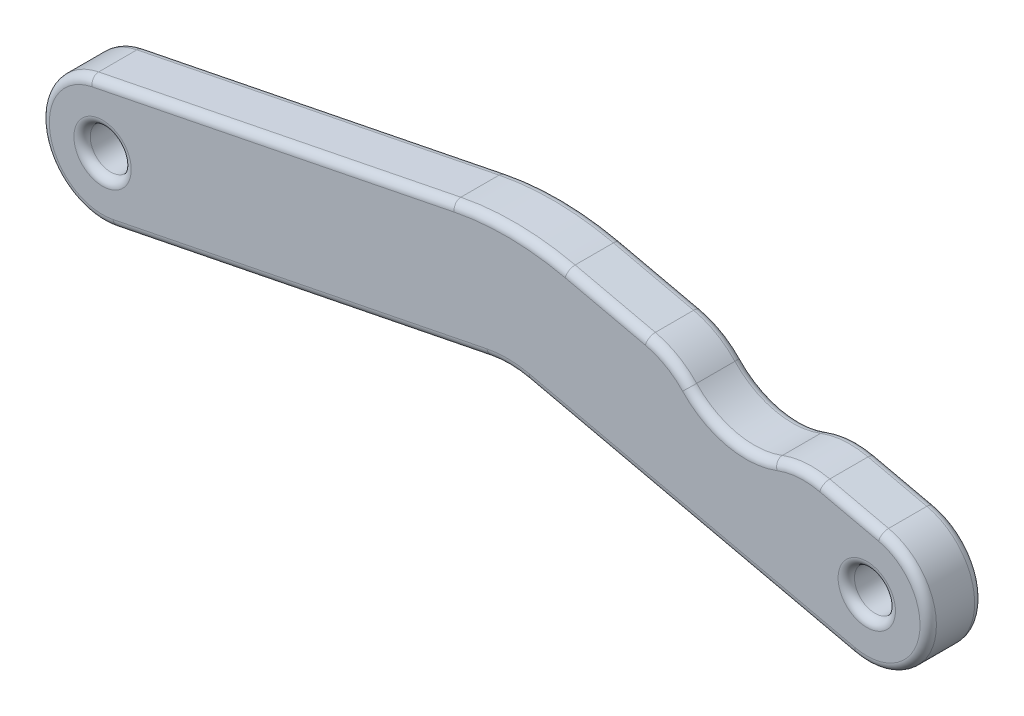
SolidWorks part; units mm, degrees
ref_plane "Front" through (0, 0, 0) normal (0, 0, 1) x (1, 0, 0)
ref_plane "Top" through (0, 0, 0) normal (0, 1, 0) x (1, 0, 0)
ref_plane "Right" through (0, 0, 0) normal (1, 0, 0) x (0, 0, -1)
sketch "Sketch1" plane through (0, 0, 0) normal (0, 0, 1) x (1, 0, 0)
  line L0 (0, 0) -> (27.9872, 0) construction
  line L1 (0, 2.25) -> (27.9872, 2.25)
  line L2 (0, -2.25) -> (27.9872, -2.25)
  circle A0 centre (0, 0) radius 0.75
  arc A1 (0, 2.25) -> (0, -2.25) centre (0, 0) ccw
  arc A2 (27.9872, -2.25) -> (27.9872, 2.25) centre (27.9872, 0) ccw
  circle A3 centre (27.9872, 0) radius 0.75
  point P3 (13.9936, 0)
  dimension "D1" = 1.5
  dimension "D2" = 27.9872
  dimension "D3" = 1.5
extrude "Boss-Extrude1" add sketch "Sketch1" along normal blind 2
sketch "Sketch2" plane through (0, 0, 0) normal (0, 0, 1) x (1, 0, 0)
  line L0 (12.0571, -0.5571) -> (14.4503, 0.4122)
  line L1 (15.3955, 0.2207) -> (16.4724, -0.5571)
  line L2 (16.4724, -0.5571) -> (17.3174, -2.6432)
  line L3 (17.3174, -2.6432) -> (12.0571, -3.2881)
  line L4 (12.0571, -3.2881) -> (12.0571, -0.5571)
  arc A0 (14.4503, 0.4122) -> (15.3955, 0.2207) centre (14.7783, -0.3977) cw
sketch "Sketch3" plane through (0, 0, 0) normal (0, 0, 1) x (1, 0, 0)
  line L0 (0.4422, -2.2061) -> (14.1398, 0.5393)
  line L1 (15.5781, 0.5204) -> (27.4873, -2.1937)
  line L2 (-0.4422, 2.2061) -> (12.8219, 4.8647)
  line L3 (17.0092, 4.8097) -> (28.4872, 2.1937)
  circle A0 centre (0, 0) radius 2.25 construction
  arc A1 (14.1398, 0.5393) -> (15.5781, 0.5204) centre (14.8148, -2.8286) cw
  arc A2 (27.4873, -2.1937) -> (28.4872, 2.1937) centre (27.9872, 0) ccw
  arc A3 (27.9872, -2.25) -> (27.9872, 2.25) centre (27.9872, 0) ccw construction
  circle A4 centre (27.9872, 0) radius 0.75 construction
  arc A5 (0.4422, -2.2061) -> (-0.4422, 2.2061) centre (0, 0) cw
  arc A6 (0, 2.25) -> (0, -2.25) centre (0, 0) ccw construction
  arc A7 (12.8219, 4.8647) -> (17.0092, 4.8097) centre (14.7871, -4.9403) cw
  dimension "D1" = 10
extrude "Cut-Extrude4" cut sketch "Sketch3" along normal through all flip side to cut
sketch "Sketch4" plane through (0, 0, 2) normal (0, 0, 1) x (1, 0, 0)
  line L4 (12.8219, 4.8647) -> (-0.4422, 2.2061)
  line L5 (28.4872, 2.1937) -> (17.0092, 4.8097)
  line L6 (15.5781, 0.5204) -> (27.4873, -2.1937)
  line L7 (0.4422, -2.2061) -> (14.1398, 0.5393)
  line L8 (12.8219, 4.8647) -> (-0.4422, 2.2061)
  line L9 (28.4872, 2.1937) -> (17.0092, 4.8097)
  line L10 (15.5781, 0.5204) -> (27.4873, -2.1937)
  line L11 (0.4422, -2.2061) -> (14.1398, 0.5393)
  circle A0 centre (27.9872, 0) radius 0.75 construction
  circle A1 centre (0, 0) radius 0.75 construction
  circle A2 centre (27.9872, 0) radius 0.75
  circle A3 centre (0, 0) radius 0.75
  arc A4 (17.0092, 4.8097) -> (12.8219, 4.8647) centre (14.7871, -4.9403) ccw
  arc A5 (27.4873, -2.1937) -> (28.4872, 2.1937) centre (27.9872, 0) ccw
  arc A6 (15.5781, 0.5204) -> (14.1398, 0.5393) centre (14.8148, -2.8286) ccw
  arc A7 (-0.4422, 2.2061) -> (0.4422, -2.2061) centre (0, 0) ccw
  arc A8 (17.0092, 4.8097) -> (12.8219, 4.8647) centre (14.7871, -4.9403) ccw
  arc A9 (27.4873, -2.1937) -> (28.4872, 2.1937) centre (27.9872, 0) ccw
  arc A10 (15.5781, 0.5204) -> (14.1398, 0.5393) centre (14.8148, -2.8286) ccw
  arc A11 (-0.4422, 2.2061) -> (0.4422, -2.2061) centre (0, 0) ccw
  dimension "D1" = 0
extrude "Boss-Extrude2" add sketch "Sketch4" against normal up to vertex
sketch3d "3DSketch2"
  line L8 (28.5539, 2.4862, 2) -> (20.7366, 4.2679, 2)
  line L9 (30.5553, 5.4776, 2) -> (31.9718, 1.7671, 2)
  line L10 (18.1052, 9.4862, 2) -> (17.7608, 10.5197, 2)
  line L11 (20.8202, 8.9829, 2) -> (18.1052, 9.4862, 2)
  arc A18 (30.4787, 0.5435, 2) -> (28.5539, 2.4862, 2) centre (27.9872, 0, 2) ccw
  arc A19 (29.7103, 7.668, 2) -> (30.5553, 5.4776, 2) centre (-281.7577, -113.7456, 2) ccw
  arc A20 (25.106, 12.1538, 2) -> (29.7103, 7.668, 2) centre (22.4753, 4.8477, 2) ccw
  arc A21 (21.1241, 8.8735, 2) -> (20.8202, 8.9829, 2) centre (20.6379, 7.9997, 2) ccw
  arc A22 (26.5449, 8.4396, 2) -> (21.1241, 8.8735, 2) centre (23.5636, 5.2719, 2) ccw
  arc A23 (25.3798, 7.2017, 2) -> (26.5449, 8.4396, 2) centre (25.9623, 7.8207, 2) ccw
  arc A24 (21.6394, 7.094, 2) -> (25.3798, 7.2017, 2) centre (23.5636, 5.2719, 2) ccw
  arc A25 (20.9991, 6.8287, 2) -> (21.6394, 7.094, 2) centre (21.0222, 7.6784, 2) ccw
  arc A26 (20.7366, 4.2679, 2) -> (20.9991, 6.8287, 2) centre (23.5636, 5.2719, 2) ccw
  spline S12 degree 3 poles (31.0836, 0.7536, 2) (30.8819, 0.6835, 2) (30.6803, 0.6135, 2) (30.4787, 0.5435, 2) knots 0 0 0 0 1 1 1 1
  spline S13 degree 3 poles (31.9718, 1.7671, 2) (31.9394, 1.656, 2) (31.8982, 1.5432, 2) (31.793, 1.3329, 2) (31.7287, 1.2339, 2) (31.5778, 1.0565, 2) (31.4894, 0.9764, 2) (31.2983, 0.8449, 2) (31.195, 0.7923, 2) (31.0836, 0.7536, 2) knots 0 0 0 0 0.25 0.25 0.5 0.5 0.75 0.75 1 1 1 1
  spline S14 degree 3 poles (21.9785, 12.5206, 2) (22.5054, 12.5209, 2) (23.0298, 12.4877, 2) (24.0747, 12.3695, 2) (24.5956, 12.2784, 2) (25.106, 12.1538, 2) knots 0 0 0 0 0.5 0.5 1 1 1 1
  spline S15 degree 3 poles (21.2302, 12.2749, 2) (21.4793, 12.3579, 2) (21.7264, 12.4476, 2) (21.9785, 12.5206, 2) knots 0 0 0 0 1 1 1 1
  spline S16 degree 3 poles (19.5527, 11.5132, 2) (19.7933, 11.7049, 2) (20.0675, 11.854, 2) (20.6399, 12.0887, 2) (20.9367, 12.1771, 2) (21.2302, 12.2749, 2) knots 0 0 0 0 0.5 0.5 1 1 1 1
  spline S17 degree 3 poles (17.7608, 10.5197, 2) (18.4099, 10.7525, 2) (19.009, 11.0801, 2) (19.5527, 11.5132, 2) knots 0 0 0 0 1 1 1 1
  point P53 (27.9872, 0, 4.55)
  point P54 (-281.7577, -113.7456, -332.2957)
  point P55 (22.4753, 4.8477, -5.7653)
  point P56 (20.6379, 7.9997, 3)
  point P57 (23.5636, 5.2719, 6.35)
  point P58 (25.9623, 7.8207, 2.85)
  point P59 (23.5636, 5.2719, -0.65)
  point P60 (21.0222, 7.6784, 2.85)
  point P61 (23.5636, 5.2719, -1)
sketch "Sketch6" plane through (0, 0, 0) normal (0, 0, 1) x (1, 0, 0)
  line L0 (28.4872, 2.1937) -> (17.0092, 4.8097) construction
  line L1 (26.3336, 2.6846) -> (28.4872, 2.1937)
  line L2 (19.946, 4.1403) -> (18.7601, 4.4106)
  line L3 (18.7601, 4.4106) -> (19.0316, 7.1775)
  line L4 (19.0316, 7.1775) -> (29.1272, 6.3891)
  line L5 (29.1272, 6.3891) -> (28.4872, 2.1937)
  circle A0 centre (23.5636, 5.2719) radius 1
  circle A1 centre (23.5636, 5.2719) radius 2.5 construction
  arc A2 (21.4578, 3.278) -> (24.5974, 2.5625) centre (23.5636, 5.2719) ccw
  arc A3 (24.5974, 2.5625) -> (26.3336, 2.6846) centre (25.6669, -0.2404) cw
  arc A4 (21.4578, 3.278) -> (19.946, 4.1403) centre (19.2794, 1.2153) ccw
  point P13 (25.2699, 2.927)
  point P14 (0, 0)
  point P20 (21.0097, 3.8979)
  dimension "D1" = 2
  dimension "D2" = 1.5
  dimension "D3" = 3
  dimension "D4" = 3
  dimension "D5" = 0.4
extrude "Cut-Extrude6" cut sketch "Sketch6" against normal through all and the other way through all
fillet "Fillet1" radius 0.3 28 edges at (28.7372, 0, 0) (0.75, 0, 0) (7.291, -0.8334, 0) (14.86, 0.606, 0) (21.5327, -0.8367, 0) (30.181, -0.5, 0) (18.4776, 4.475, 2) (27.4104, 2.4392, 2) (14.9184, 5.0588, 2) (14.9184, 5.0588, 0) (6.1898, 3.5354, 2) (6.1898, 3.5354, 0) (-2.2061, -0.4422, 0) (28.7372, 0, 2) (0.75, 0, 2) (30.181, -0.5, 2) (21.5327, -0.8367, 2) (14.86, 0.606, 2) (7.291, -0.8334, 2) (-2.2061, -0.4422, 2) (22.9192, 2.4444, 0) (20.7658, 3.8212, 2) (22.9192, 2.4444, 2) (25.4565, 2.7522, 2)
